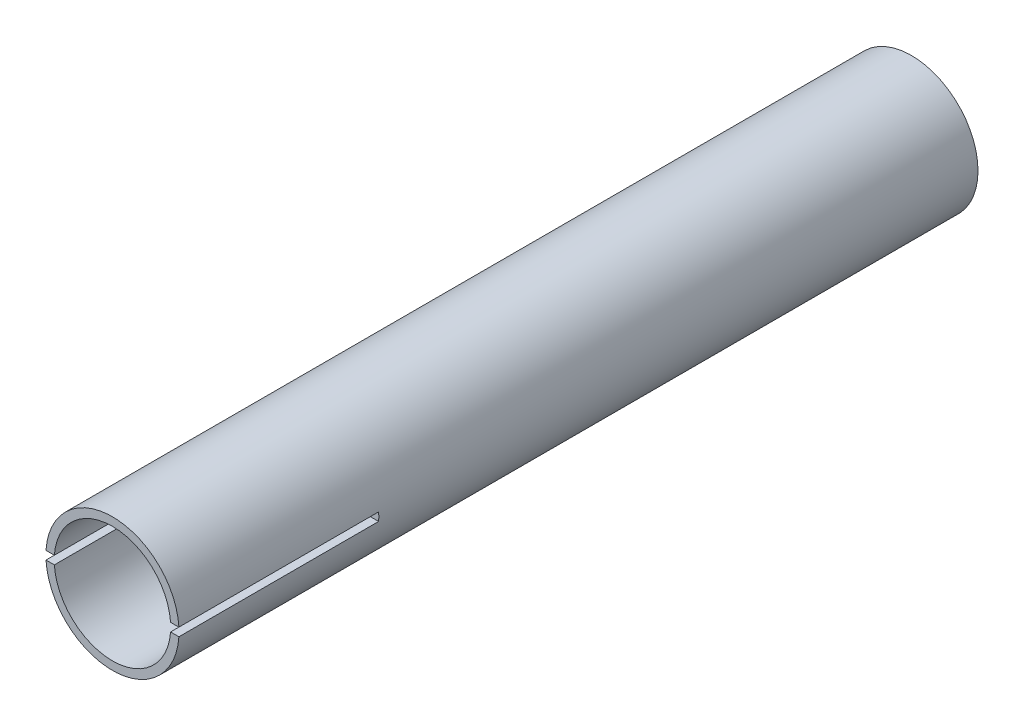
SolidWorks part; units mm, degrees
ref_plane "Front" through (0, 0, 0) normal (0, 0, 1) x (1, 0, 0)
ref_plane "Top" through (0, 0, 0) normal (0, 1, 0) x (1, 0, 0)
ref_plane "Right" through (0, 0, 0) normal (1, 0, 0) x (0, 0, -1)
sketch "Sketch1" plane through (0, 0, 0) normal (0, 0, 1) x (1, 0, 0)
  circle A0 centre (0, 0) radius 11.1125
  circle A1 centre (0, 0) radius 12.7
  dimension "D1" = 25.4
  dimension "D2" = 22.225
extrude "Extrude1" add sketch "Sketch1" along normal blind 152.4
sketch "Sketch2" plane through (0, 0, 0) normal (1, 0, 0) x (0, 0, -1)
  line L0 (-152.4, 12.7) -> (-152.4, -12.7) construction
  line L1 (-114.3, 0.7938) -> (-152.4, 0.7938)
  line L2 (-114.3, 0.7938) -> (-114.3, -0.7937)
  line L3 (-114.3, -0.7937) -> (-152.4, -0.7938)
  line L4 (-152.4, 0.7938) -> (-152.4, -0.7938)
  point P6 (-114.3, 0)
  dimension "D1" = 1.5875
  dimension "D2" = 38.1
extrude "Cut-Extrude1" cut sketch "Sketch2" against normal up to next and the other way up to next
